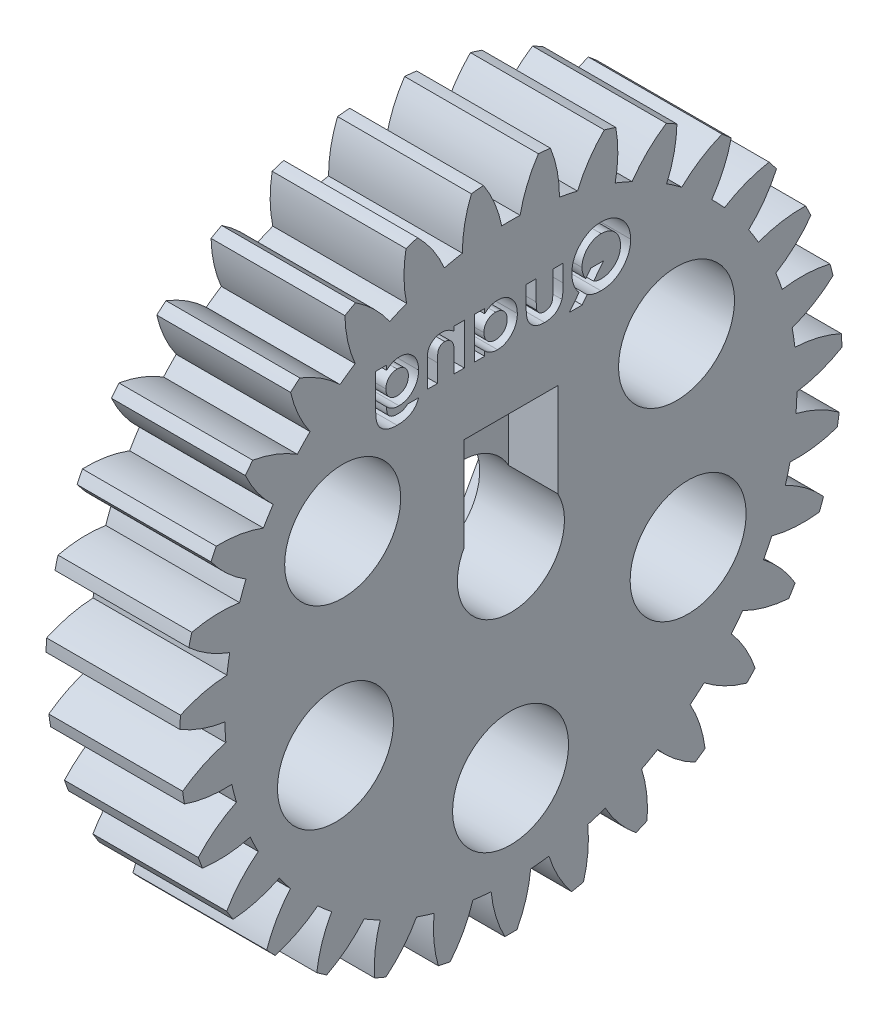
SolidWorks part; units mm, degrees
ref_plane "Plane1" through (0, 0, 0) normal (0, 0, 1) x (1, 0, 0)
ref_plane "Plane2" through (0, 0, 0) normal (0, 1, 0) x (1, 0, 0)
ref_plane "Plane3" through (0, 0, 0) normal (1, 0, 0) x (0, 0, -1)
sketch "HoldingSke" plane through (0, 0, 0) normal (0, 1, 0) x (1, 0, 0)
  line L0 (0, 0) -> (0.381, -0.2289)
  line L1 (-15, 0) -> (100, 0) construction
  line L2 (0, 0) -> (-2.1039, 2.3779)
  line L3 (0, 0) -> (-11.863, 4.5341)
  line L4 (0, 0) -> (7.4025, 4.4479)
  line L5 (0, 0) -> (-46.8476, -17.4728)
  line L6 (0, 0) -> (-12.4344, -8.3896)
  line L7 (-2.1039, 2.3779) -> (8.6586, 51.2059)
  line L8 (-76.2, 54.61) -> (-76.1, 54.61)
  line L9 (-71.009, 38.7566) -> (-53.1078, 45.2721)
  line L10 (-76.2, 71.12) -> (104.1128, 71.12)
  line L11 (0, 0) -> (-15, 0)
  line L12 (-76.2, 101.6) -> (-76.123, 101.6)
  line L13 (24.9733, 27.94) -> (52.9518, 28.4284)
  line L14 (24.9733, 27.94) -> (24.9743, 27.94)
  line L15 (24.9733, 27.94) -> (100.4006, 29.5858)
  line L16 (-63.627, -2.25) -> (-12.827, -2.25)
  circle A0 centre (0, 0) radius 0.4
  circle A1 centre (0, 0) radius 32.0615
  circle A2 centre (0, 0) radius 37.5
  circle A3 centre (0, 0) radius 0.4
  dimension "MHD" = 64.123
  dimension "Hub_dia" = 75
  dimension "Bore" = 0.8
  dimension "MBD" = 0.8
  dimension "Num_teeth" = 31
  dimension "Pitch_radius" = 180.3128
  dimension "Pitch" = 0.4444
  dimension "Width" = 15
  dimension "Overall_len" = 50
  dimension "Show_teeth" = 31
  dimension "Thickness" = 15
  dimension "OAL" = 50.0001
  dimension "T_dim" = 0.1
  dimension "Ap" = 20
  dimension "H" = 19.05
  dimension "Backlash" = 0.077
  dimension "Addendum_fac" = 1
  dimension "Dedendum_fac" = 1.25
  dimension "Clearance_fac" = 0.25
  dimension "Dedendum_add" = 0.001
  dimension "Module" = 2.25
sketch "BasProSke" plane through (0, 0, 0) normal (0, 1, 0) x (1, 0, 0)
  line L0 (-10, 0) -> (60, 0) construction
  line L1 (0, 0) -> (0, 37.125)
  line L2 (0, 0) -> (15, 0)
  line L3 (15, 0) -> (15, 37.125)
  line L4 (15, 37.125) -> (0, 37.125)
  dimension "Diameter" = 74.25
  dimension "Thickness" = 15
revolve "Base-Revolve" add sketch "BasProSke" angle 360 about L0
sketch "TooCutSke" plane through (0, 0, 0) normal (1, 0, 0) x (0, 0, -1)
  line L1 (0, 0) -> (0, 107) construction
  line L2 (0, 0) -> (-1.9011, 34.8231) construction
  line L3 (0, 0) -> (-7.0488, 69.3161) construction
  line L4 (-1.9011, 34.8231) -> (-3.5244, 34.6581) construction
  arc A0 (1.0309, 32.0449) -> (-1.0309, 32.0449) centre (0, 0) ccw
  arc A1 (3.0958, 37.0212) -> (-3.0958, 37.0212) centre (0, 0) ccw
  circle A2 centre (0, 0) radius 34.875 construction
  circle A3 centre (0, 0) radius 32.7718 construction
  arc A4 (-1.0309, 32.0449) -> (-3.0958, 37.0212) centre (-14.7056, 29.2871) ccw
  arc A5 (3.0958, 37.0212) -> (1.0309, 32.0449) centre (14.7056, 29.2871) ccw
  dimension "Root_dia" = 64.123
  dimension "Overcut_dia" = 74.3008
  dimension "Pitch_dia" = 69.75
  dimension "Base_dia" = 65.5436
  dimension "Flank_rad" = 13.95
  dimension "Half_ang" = 5.806
  dimension "Half_CT" = 1.6316
extrude "ToothCut" cut sketch "TooCutSke" along normal through all
fillet "Breaks" [suppressed] radius 0.045
fillet "RootFillets" [suppressed] radius 0.5635
pattern_circular "TeethCuts" count 31 over 360 about axis through (0, 0, 0) along (1, 0, 0) of "ToothCut", "RootFillets", "Breaks"
sketch "HubNeaOneSke" plane through (0, 0, 0) normal (-1, 0, 0) x (0, 0, 1)
  circle A0 centre (0, 0) radius 32.0615
  dimension "Diameter" = 64.123
extrude "HubNearOne" [suppressed] add sketch "HubNeaOneSke" along normal blind 35.0001
sketch "HubNeaBotSke" plane through (0, 0, 0) normal (-1, 0, 0) x (0, 0, 1)
  circle A0 centre (0, 0) radius 32.0615
  dimension "Diameter" = 64.123
extrude "HubNearBoth" [suppressed] add sketch "HubNeaBotSke" along normal blind 17.5
ref_plane "FarPln" through (15, 0, 0) normal (1, 0, 0) x (0, 0, -1)
sketch "HubFarSke" plane through (15, 0, 0) normal (1, 0, 0) x (0, 0, -1)
  circle A0 centre (0, 0) radius 32.0615
  dimension "Diameter" = 64.123
extrude "HubFar" [suppressed] add sketch "HubFarSke" along normal blind 17.5
sketch "BorSke" plane through (0, 0, 0) normal (1, 0, 0) x (0, 0, -1)
  circle A0 centre (0, 0) radius 6
  dimension "Diameter" = 12
extrude "Bore" cut sketch "BorSke" along normal mid plane 100.0001
sketch "KeySke" plane through (0, 0, 0) normal (1, 0, 0) x (0, 0, -1)
  line L0 (-0.05, 0) -> (-0.05, 0.5)
  line L1 (-0.05, 0.5) -> (0.05, 0.5)
  line L2 (0.05, 0.5) -> (0.05, 0)
  line L3 (0, 0) -> (0, 34) construction
  line L4 (-0.05, 0) -> (0.05, 0)
  dimension "Offset" = 0.5
  dimension "Width" = 0.1
extrude "Keyway" [suppressed] cut sketch "KeySke" along normal mid plane 100.0001
pattern_circular "Keyway2" [suppressed] count 2 every 90 about axis through (-10, 0, 0) along (1, 0, 0)
sketch "Sketch1" plane through (0, 0, 0) normal (-1, 0, 0) x (0, 0, 1)
  text T0 "<b>Quang</b>" font "Century Gothic" height 6.35
sketch "Sketch2" plane through (15, 0, 0) normal (1, 0, 0) x (0, 0, -1)
  line L2 (-5.25, 2.9047) -> (-5.25, 13.4047)
  line L3 (-5.25, 13.4047) -> (5.25, 13.4047)
  line L4 (5.25, 2.9047) -> (5.25, 13.4047)
  arc A0 (-5.25, 2.9047) -> (5.25, 2.9047) centre (0, 0) ccw
  circle A1 centre (0, 0) radius 6 construction
  dimension "D1" = 0
  dimension "D5" = 10.5
  dimension "D6" = 10.5
extrude "Cut-Extrude1" cut sketch "Sketch2" against normal blind 5.5
sketch "Sketch8" plane through (0, 0, 0) normal (-1, 0, 0) x (0, 0, 1)
  line L1 (13.854, -0.2947) -> (7.1504, 11.8322)
  line L2 (7.1504, 11.8322) -> (-6.7036, 12.0901)
  line L3 (-6.7036, 12.0901) -> (-13.854, 0.2211)
  line L4 (-13.854, 0.2211) -> (-7.1504, -11.9057)
  line L5 (-7.1504, -11.9057) -> (6.7036, -12.1637)
  line L6 (6.7036, -12.1637) -> (13.854, -0.2947)
  circle A0 centre (0, -0.0368) radius 12 construction
  circle A1 centre (0, 0) radius 6 construction
  dimension "D1" = 0
  dimension "D2" = 24
extrude "Cut-Extrude5" cut sketch "Sketch8" against normal blind 5.5
sketch "Sketch10" plane through (0, 0, 0) normal (-1, 0, 0) x (0, 0, 1)
  line L0 (-6.7036, 12.0901) -> (-13.854, 0.2211) construction
  line L1 (13.854, -0.2947) -> (7.1504, 11.8322) construction
  line L2 (6.7036, -12.1637) -> (13.854, -0.2947) construction
  line L3 (-7.1504, -11.9057) -> (6.7036, -12.1637) construction
  line L4 (-13.854, 0.2211) -> (-7.1504, -11.9057) construction
  circle A0 centre (-19.8634, -9.5779) radius 6.5
  circle A1 centre (0.0405, -22.0413) radius 6.5
  circle A2 centre (19.6658, -10.0262) radius 6.5
  circle A3 centre (18.8582, 11.3227) radius 6.5
  circle A4 centre (-18.5625, 11.7841) radius 6.5
  dimension "D6" = 13
  dimension "D7" = 13
  dimension "D8" = 13
  dimension "D9" = 13
  dimension "D10" = 13
  dimension "D1" = 10
  dimension "D2" = 10
  dimension "D3" = 10
  dimension "D4" = 10
  dimension "D5" = 10
extrude "Cut-Extrude6" cut sketch "Sketch10" against normal through all
extrude "Cut-Extrude7" cut sketch "Sketch1" against normal through all
equation "' \"Module@HoldingSke\" = 6.35"
equation "' \"Num_teeth@HoldingSke\" = 12"
equation "' \"Ap@HoldingSke\" =  20"
equation "' \"Width@HoldingSke\" = 0.5 * 25.4"
equation "' \"Hub_dia@HoldingSke\"= 1 * 25.4"
equation "' \"Overall_len@HoldingSke\" = 1.0 * 25.4"
equation "' \"Bore@HoldingSke\" = 0.75 * 25.4"
equation "' \"T_dim@HoldingSke\" = 0.1 * 25.4"
equation "' \"Width@KeySke\" = 0.25 * 25.4"
equation "' \"Show_teeth@HoldingSke\" = 13"
equation "' \"Backlash@HoldingSke\" = 0.009 * 25.4"
equation "' \"Addendum_fac@HoldingSke\" = 1.0"
equation "' \"Dedendum_fac@HoldingSke\" = 1.25"
equation "' \"Dedendum_add@HoldingSke\" = 0.00005 * 25.4"
equation "' \"Clearance_fac@HoldingSke\" = 0.25"
equation "\"Pitch@HoldingSke\" = 1 / \"Module@HoldingSke\""
equation "\"Overcut_dia@TooCutSke\" = (\"Num_teeth@HoldingSke\" + 2 * \"Addendum_fac@HoldingSke\") / \"Pitch@HoldingSke\" + 0.002 * 25.4"
equation "\"Pitch_dia@TooCutSke\" = \"Num_teeth@HoldingSke\" / \"Pitch@HoldingSke\""
equation "\"Base_dia@TooCutSke\" = \"Num_teeth@HoldingSke\" / \"Pitch@HoldingSke\" * cos((\"Ap@HoldingSke\"  * 3.14159265 / 180))"
equation "\"Root_dia@TooCutSke\" = (\"Num_teeth@HoldingSke\" + 2) / \"Pitch@HoldingSke\" - 2 * (\"Addendum_fac@HoldingSke\" + \"Dedendum_fac@HoldingSke\") / \"Pitch@HoldingSke\" - \"Dedendum_add@HoldingSke\" * 2"
equation "\"Half_ang@TooCutSke\" = 180 / \"Num_teeth@HoldingSke\""
equation "\"Half_CT@TooCutSke\" = \"Num_teeth@HoldingSke\" / \"Pitch@HoldingSke\" * sin((3.14159265 / 2 / \"Num_teeth@HoldingSke\")) / 2 - 7 * \"Backlash@HoldingSke\" / 4"
equation "\"Flank_rad@TooCutSke\" = \"Num_teeth@HoldingSke\" / \"Pitch@HoldingSke\" / 5"
equation "\"Radius@RootFillets\" = \"Clearance_fac@HoldingSke\" / \"Pitch@HoldingSke\" + \"Dedendum_add@HoldingSke\""
equation "\"Break_rad@Breaks\" = 0.02 / \"Pitch@HoldingSke\""
equation "\"Thickness@HoldingSke\" = \"Width@HoldingSke\""
equation "\"OAL@HoldingSke\" = \"Thickness@HoldingSke\""
equation "\"MHD@HoldingSke\" = (\"Num_teeth@HoldingSke\" + 2) / \"Pitch@HoldingSke\" - 2 * (\"Addendum_fac@HoldingSke\" + \"Dedendum_fac@HoldingSke\")  / \"Pitch@HoldingSke\" - \"Dedendum_add@HoldingSke\" * 2"
equation "\"MBD@HoldingSke\" = (\"Num_teeth@HoldingSke\" + 2) / \"Pitch@HoldingSke\" - 2 * (\"Addendum_fac@HoldingSke\" + \"Dedendum_fac@HoldingSke\")  / \"Pitch@HoldingSke\" - \"Dedendum_add@HoldingSke\" * 2 - 0.002 * 25.4"
equation "\"MHD@HoldingSke\" = ((sgn( \"MHD@HoldingSke\" - \"Hub_dia@HoldingSke\" )-1)*( \"MHD@HoldingSke\" - \"Hub_dia@HoldingSke\" ))/-2+ \"Hub_dia@HoldingSke\""
equation "\"MBD@HoldingSke\" = ((sgn( \"MBD@HoldingSke\" - \"Bore@HoldingSke\" )-1)*( \"MBD@HoldingSke\" - \"Bore@HoldingSke\" ))/-2+ \"Bore@HoldingSke\""
equation "\"OAL@HoldingSke\" = ((sgn( \"OAL@HoldingSke\" - \"Overall_len@HoldingSke\" )+1)*( \"OAL@HoldingSke\" - \"Overall_len@HoldingSke\" ))/2 + \"Overall_len@HoldingSke\" + 0.000002 * 25.4"
equation "\"Num_teeth@TeethCuts\" = int( \"Show_teeth@HoldingSke\" ) + 1"
equation "\"Num_teeth@TeethCuts\" = ((sgn( \"Num_teeth@TeethCuts\" - \"Num_teeth@HoldingSke\" )-1)*( \"Num_teeth@TeethCuts\" - \"Num_teeth@HoldingSke\" ))/-2+ \"Num_teeth@HoldingSke\""
equation "\"Num_teeth@TeethCuts\" = ((sgn( \"Num_teeth@TeethCuts\" - 2.0)+1)*( \"Num_teeth@TeethCuts\" - 2.0))/2 +2.0"
equation "\"Angle@TeethCuts\" = 360.0 / \"Num_teeth@HoldingSke\""
equation "\"Diameter@BasProSke\" = (\"Num_teeth@HoldingSke\" + 2 * \"Addendum_fac@HoldingSke\") / \"Pitch@HoldingSke\""
equation "\"Thickness@BasProSke\"  = \"Thickness@HoldingSke\""
equation "' \"Fillet_rad@BasProSke\" =  \"Thickness@HoldingSke\" * 0.05"
equation "\"MHD@HoldingSke\" = ((sgn( \"MHD@HoldingSke\" - \"Root_dia@TooCutSke\" )-1)*( \"MHD@HoldingSke\" - \"Root_dia@TooCutSke\" ))/-2+ \"Root_dia@TooCutSke\""
equation "\"Diameter@HubNeaOneSke\" = \"MHD@HoldingSke\""
equation "\"Length@HubNearOne\" = \"OAL@HoldingSke\" - \"Thickness@BasProSke\""
equation "\"Diameter@HubNeaBotSke\" = \"MHD@HoldingSke\""
equation "\"Length@HubNearBoth\" = ( \"OAL@HoldingSke\" - \"Thickness@BasProSke\" ) / 2.0"
equation "\"Thickness@FarPln\" = \"Thickness@BasProSke\""
equation "\"Diameter@HubFarSke\" = \"MHD@HoldingSke\""
equation "\"Length@HubFar\" = ( \"OAL@HoldingSke\" - \"Thickness@BasProSke\" ) / 2.0"
equation "\"Diameter@BorSke\"=12"
equation "\"D1@Bore\" = \"OAL@HoldingSke\" * 2.0"
equation "\"D1@Keyway\" = \"OAL@HoldingSke\" * 2.0"
equation "\"Offset@KeySke\" = \"T_dim@HoldingSke\" + \"MBD@HoldingSke\" / 2.0"
